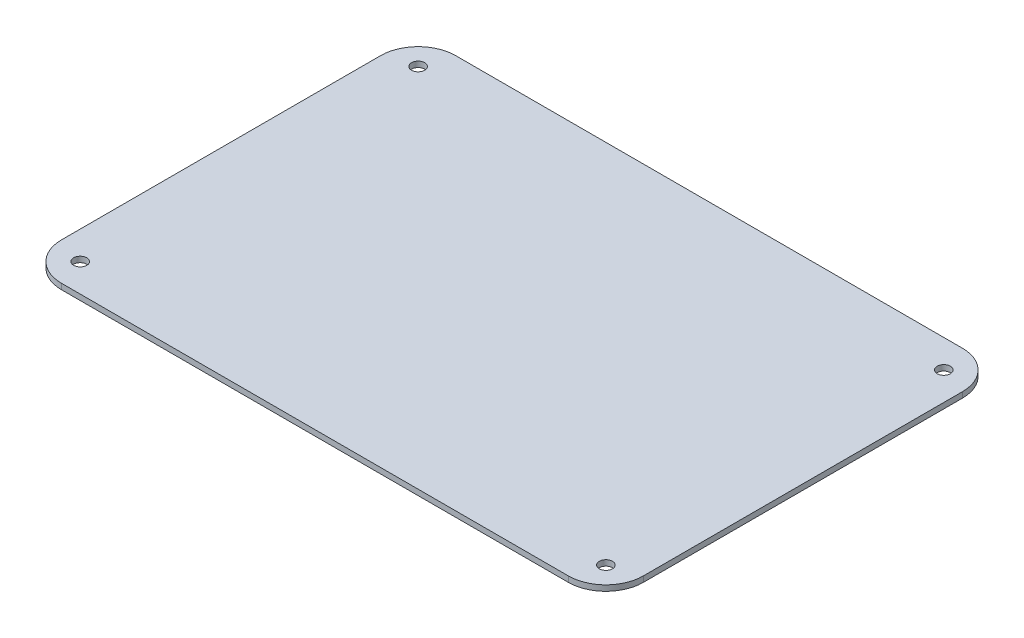
SolidWorks part; units mm, degrees
ref_plane "Front Plane" through (0, 0, 0) normal (0, 0, 1) x (1, 0, 0)
ref_plane "Top Plane" through (0, 0, 0) normal (0, 1, 0) x (1, 0, 0)
ref_plane "Right Plane" through (0, 0, 0) normal (1, 0, 0) x (0, 0, -1)
sketch "Sketch1" plane through (0, 0, 0) normal (0, 1, 0) x (1, 0, 0)
  line L1 (155, 105) -> (-155, 105)
  line L2 (155, 105) -> (155, -105)
  line L3 (155, -105) -> (-155, -105)
  line L4 (-155, 105) -> (-155, -105)
  line L5 (155, 105) -> (-155, -105) construction
  line L6 (155, -105) -> (-155, 105) construction
  circle A0 centre (-140, 90) radius 3.5
  circle A1 centre (140, 90) radius 3.5
  circle A2 centre (140, -90) radius 3.5
  circle A3 centre (-140, -90) radius 3.5
  point P0 (0, 0)
  dimension "D3" = 15
  dimension "D4" = 7
  dimension "D5" = 15
  dimension "D6" = 15
  dimension "D7" = 15
  dimension "D8" = 15
  dimension "D9" = 15
  dimension "D10" = 15
  dimension "D11" = 15
  dimension "D1" = 310
  dimension "D2" = 210
extrude "Boss-Extrude1" add sketch "Sketch1" along normal blind 3
fillet "Fillet1" radius 20 4 edges at (155, 1.5, 105) (155, 1.5, -105) (-155, 1.5, -105) (-155, 1.5, 105)
